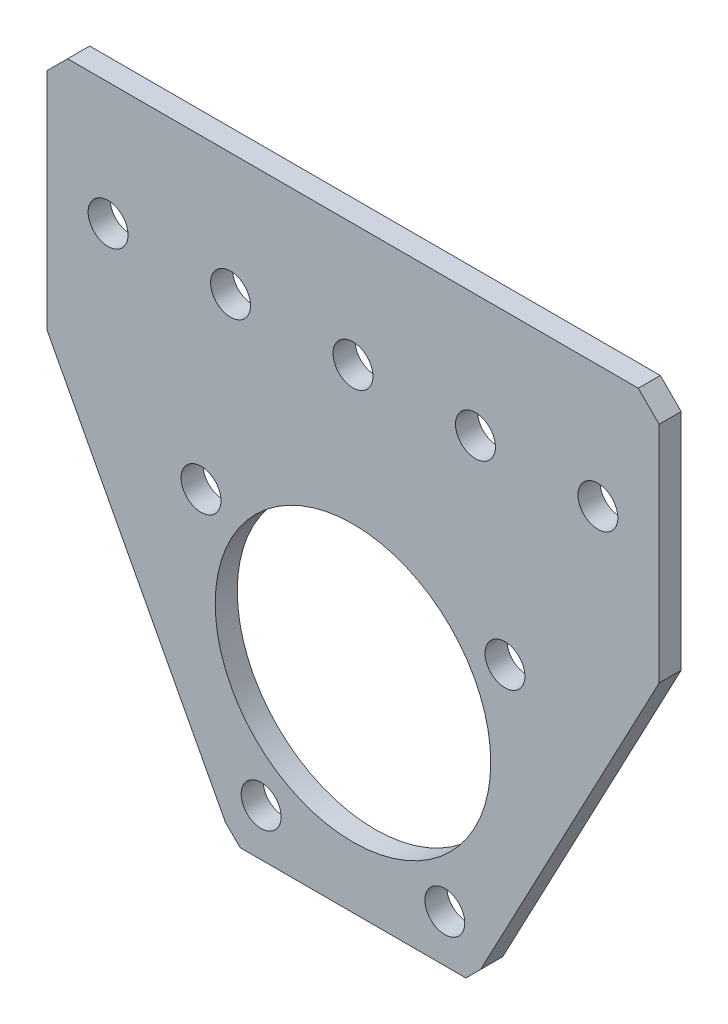
SolidWorks part; units mm, degrees
ref_plane "Front Plane" through (0, 0, 0) normal (0, 0, 1) x (1, 0, 0)
ref_plane "Top Plane" through (0, 0, 0) normal (0, 1, 0) x (1, 0, 0)
ref_plane "Right Plane" through (0, 0, 0) normal (1, 0, 0) x (0, 0, -1)
ref_plane "Plane1" through (0, 0, 0) normal (0, 0, -1) x (-1, 0, 0)
sketch "Sketch1" plane through (0, 0, 0) normal (0, 0, -1) x (-1, 0, 0)
  line L0 (-29.591, 41.275) -> (-31.75, 39.116)
  line L1 (-31.75, 39.116) -> (-31.75, 15.875)
  line L2 (-31.75, 15.875) -> (-13.2358, -19.1109)
  line L3 (-13.2358, -19.1109) -> (-11.7091, -20.6375)
  line L4 (-11.7091, -20.6375) -> (11.7091, -20.6375)
  line L5 (11.7091, -20.6375) -> (13.2358, -19.1109)
  line L6 (13.2358, -19.1109) -> (31.75, 15.875)
  line L7 (31.75, 15.875) -> (31.75, 39.116)
  line L8 (31.75, 39.116) -> (29.591, 41.275)
  line L9 (29.591, 41.275) -> (-29.591, 41.275)
  circle A0 centre (-15.7603, 9.525) radius 2.0701
  circle A1 centre (9.525, -15.7603) radius 2.0701
  circle A2 centre (-12.7, 28.575) radius 2.0701
  circle A3 centre (12.7, 28.575) radius 2.0701
  circle A4 centre (25.4, 28.575) radius 2.0701
  circle A5 centre (0, 0) radius 14.2875
  circle A6 centre (-25.4, 28.575) radius 2.0701
  circle A7 centre (0, 28.575) radius 2.0701
  circle A8 centre (15.7603, 9.525) radius 2.0701
  circle A9 centre (-9.525, -15.7603) radius 2.0701
extrude "Boss-Extrude1" add sketch "Sketch1" against normal blind 2.286
